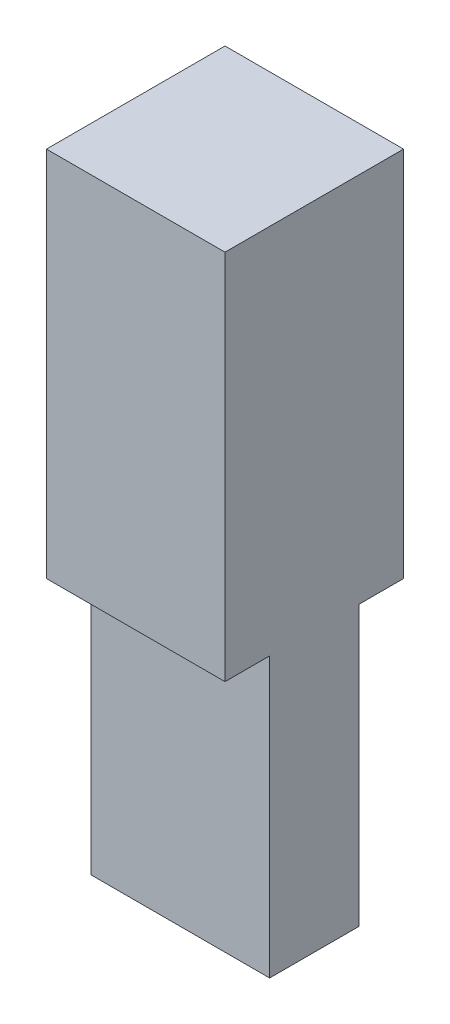
SolidWorks part; units mm, degrees
ref_plane "Front Plane" through (0, 0, 0) normal (0, 0, 1) x (1, 0, 0)
ref_plane "Top Plane" through (0, 0, 0) normal (0, 1, 0) x (1, 0, 0)
ref_plane "Right Plane" through (0, 0, 0) normal (1, 0, 0) x (0, 0, -1)
sketch "Sketch2" plane through (0, 0, 0) normal (1, 0, 0) x (0, 0, -1)
  line L0 (0, 0) -> (-1.524, 0)
  line L1 (-1.524, 0) -> (-1.524, 9.525)
  line L2 (-1.524, 9.525) -> (-3.048, 9.525)
  line L3 (-3.048, 9.525) -> (-3.048, 22.225)
  line L4 (-3.048, 22.225) -> (3.048, 22.225)
  line L5 (3.048, 22.225) -> (3.048, 9.525)
  line L6 (3.048, 9.525) -> (1.524, 9.525)
  line L7 (1.524, 9.525) -> (1.524, 0)
  line L8 (1.524, 0) -> (0, 0)
  dimension "D1" = 3.048
  dimension "D2" = 9.525
  dimension "D3" = 12.7
  dimension "D4" = 1.524
extrude "Boss-Extrude1" add sketch "Sketch2" along normal blind 6.096
